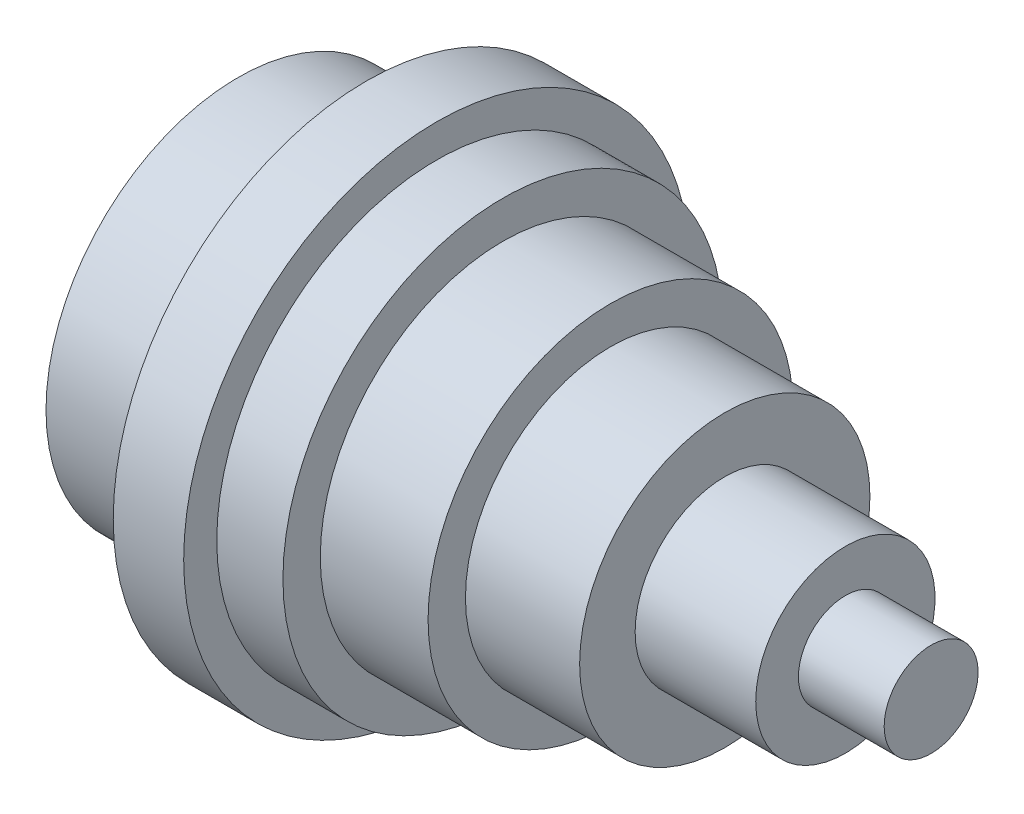
SolidWorks part; units mm, degrees
ref_plane "Front Plane" through (0, 0, 0) normal (0, 0, 1) x (1, 0, 0)
ref_plane "Top Plane" through (0, 0, 0) normal (0, 1, 0) x (1, 0, 0)
ref_plane "Right Plane" through (0, 0, 0) normal (1, 0, 0) x (0, 0, -1)
sketch "Sketch2" plane through (0, 0, 0) normal (0, 0, 1) x (1, 0, 0)
  line L0 (-108.212, 0) -> (74.1591, 0) construction
  line L1 (0, 0) -> (0, -5)
  line L2 (0, -5) -> (-9.1294, -5)
  line L3 (-9.1294, -5) -> (-9.1294, -9.5451)
  line L4 (-9.1294, -9.5451) -> (-21.9692, -9.5451)
  line L5 (-21.9692, -9.5451) -> (-21.9692, -15.4537)
  line L6 (-21.9692, -15.4537) -> (-34.1273, -15.4537)
  line L7 (-34.1273, -15.4537) -> (-34.1273, -19.4306)
  line L8 (-34.1273, -19.4306) -> (-45.6036, -19.4306)
  line L9 (-45.6036, -19.4306) -> (-45.6036, -23.4076)
  line L10 (-45.6036, -23.4076) -> (-52.6485, -23.4076)
  line L11 (-52.6485, -23.4076) -> (-52.6485, -26.93)
  line L12 (-52.6485, -26.93) -> (-60.1478, -26.93)
  line L13 (-60.1478, -26.93) -> (-60.1478, -20.4533)
  line L14 (-60.1478, -20.4533) -> (-73.7831, -20.4533)
  line L15 (-73.7831, -20.4533) -> (-73.7831, 0)
  line L16 (-73.7831, 0) -> (0, 0)
  dimension "D1" = 5
  dimension "D2" = 10
  dimension "D3" = 20
  dimension "D4" = 30
  dimension "D5" = 40
  dimension "D6" = 50
  dimension "D7" = 80
  dimension "D8" = 50
  dimension "D9" = 20
  dimension "D10" = 20
  dimension "D11" = 20
  dimension "D12" = 20
  dimension "D13" = 20
  dimension "D14" = 20
  dimension "D15" = 40
revolve "Revolve1" add sketch "Sketch2" angle 360 about L0
